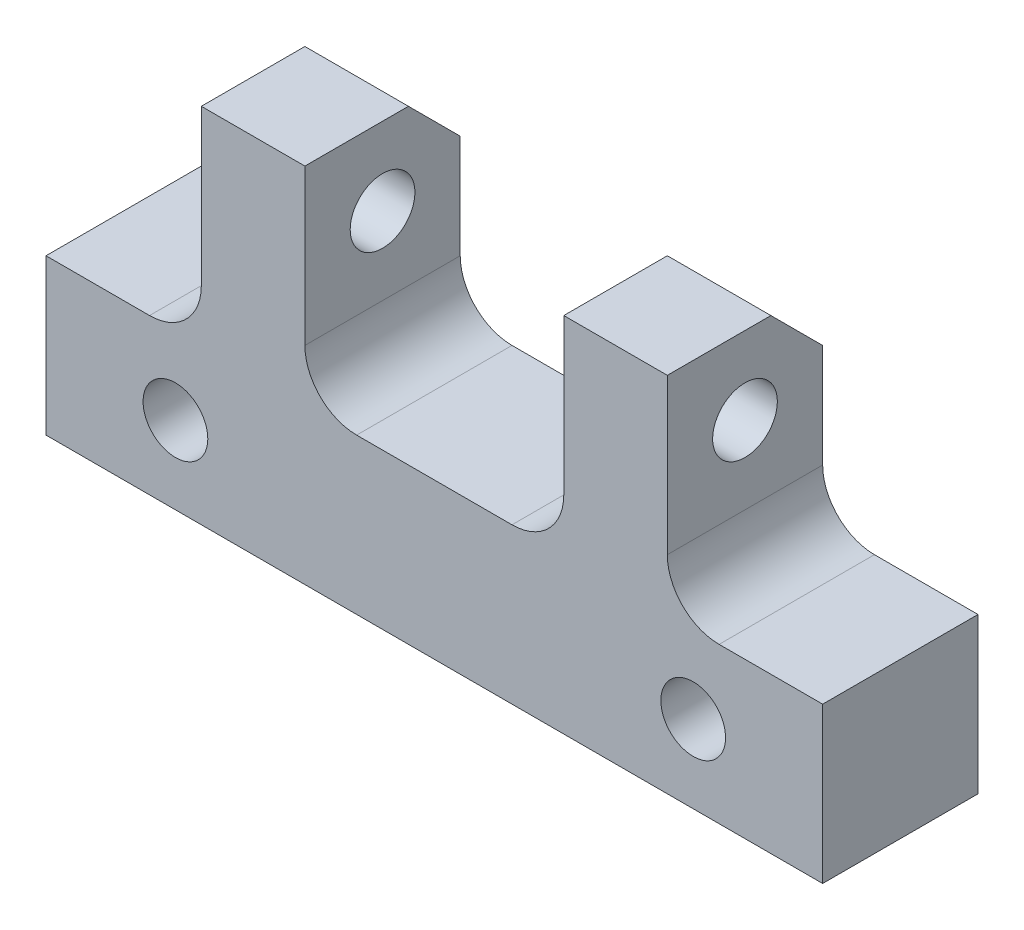
SolidWorks part; units mm, degrees
material "6061 合金"
ref_plane "前视基准面" through (0, 0, 0) normal (0, 0, 1) x (1, 0, 0)
ref_plane "上视基准面" through (0, 0, 0) normal (0, 1, 0) x (1, 0, 0)
ref_plane "右视基准面" through (0, 0, 0) normal (1, 0, 0) x (0, 0, -1)
sketch "草图1" plane through (0, 0, 0) normal (0, 0, 1) x (1, 0, 0)
  line L0 (0, 6.0777) -> (0, -6) construction
  line L1 (-15, -6) -> (15, -6)
  line L4 (5, 8) -> (5, 0)
  line L5 (5, 0) -> (-5, 0)
  line L6 (-5, 0) -> (-5, 8)
  line L9 (-5, 8) -> (-9, 8)
  line L10 (-9, 8) -> (-9, 0)
  line L11 (-9, 0) -> (-15, 0)
  line L12 (-15, 0) -> (-15, -6)
  line L13 (5, 8) -> (9, 8)
  line L14 (9, 8) -> (9, 0)
  line L15 (9, 0) -> (15, 0)
  line L16 (15, 0) -> (15, -6)
  circle A0 centre (-10, -3) radius 1.25
  circle A1 centre (10, -3) radius 1.25
  dimension "D3" = 2.5
  dimension "D1" = 10
  dimension "D2" = 6
  dimension "D4" = 8
  dimension "D5" = 30
  dimension "D6" = 20
  dimension "D7" = 4
  dimension "D8" = 3
extrude "凸台-拉伸1" add sketch "草图1" along normal blind 6
cosmetic thread "装饰螺纹线3" parameters "D2"=3
cosmetic thread "装饰螺纹线4" parameters "D2"=3
chamfer "倒角1" distance 2 angle 45 2 edges at (7, 8, 0) (-7, 8, 0)
sketch "草图2" plane through (0, 0, 0) normal (1, 0, 0) x (0, 0, -1)
  line L0 (-3, -6) -> (-3, 8) construction
  line L1 (-6, -6) -> (0, -6) construction
  line L2 (-6, 8) -> (-2, 8) construction
  circle A0 centre (-3, 5) radius 1.25
  dimension "D1" = 2.5
  dimension "D2" = 5
extrude "切除-拉伸1" cut sketch "草图2" against normal through all both and the other way through all
cosmetic thread "装饰螺纹线1" parameters "D2"=3
cosmetic thread "装饰螺纹线2" parameters "D2"=3
fillet "圆角1" radius 2 4 edges at (5, 0, 3) (-5, 0, 3) (9, 0, 3) (-9, 0, 3)
